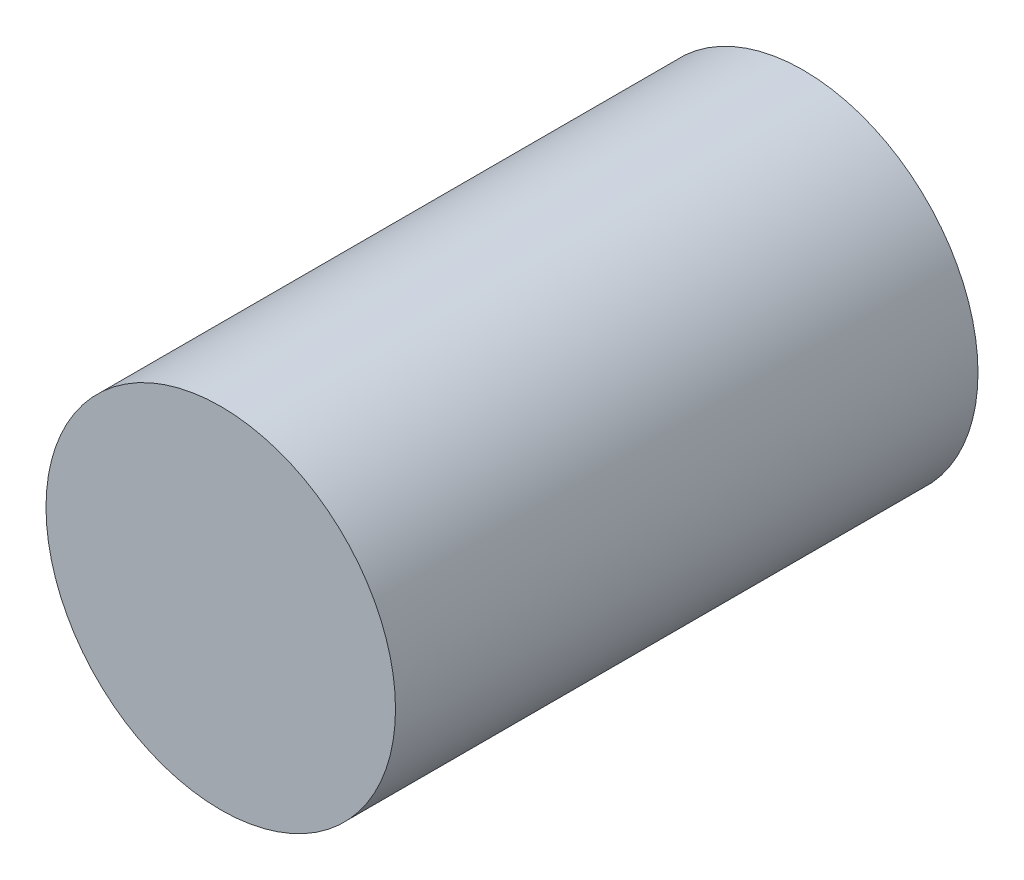
SolidWorks part; units mm, degrees
ref_plane "Front" through (0, 0, 0) normal (0, 0, 1) x (1, 0, 0)
ref_plane "Top" through (0, 0, 0) normal (0, 1, 0) x (1, 0, 0)
ref_plane "Right" through (0, 0, 0) normal (1, 0, 0) x (0, 0, -1)
sketch "Sketch1" plane through (0, 0, 0) normal (0, 0, 1) x (1, 0, 0)
  circle A1 centre (181.0719, 170.6692) radius 1.5
  point P2 (181.0719, 170.6692)
  dimension "D1" = 3
extrude "Boss-Extrude1" add sketch "Sketch1" against normal blind 5
